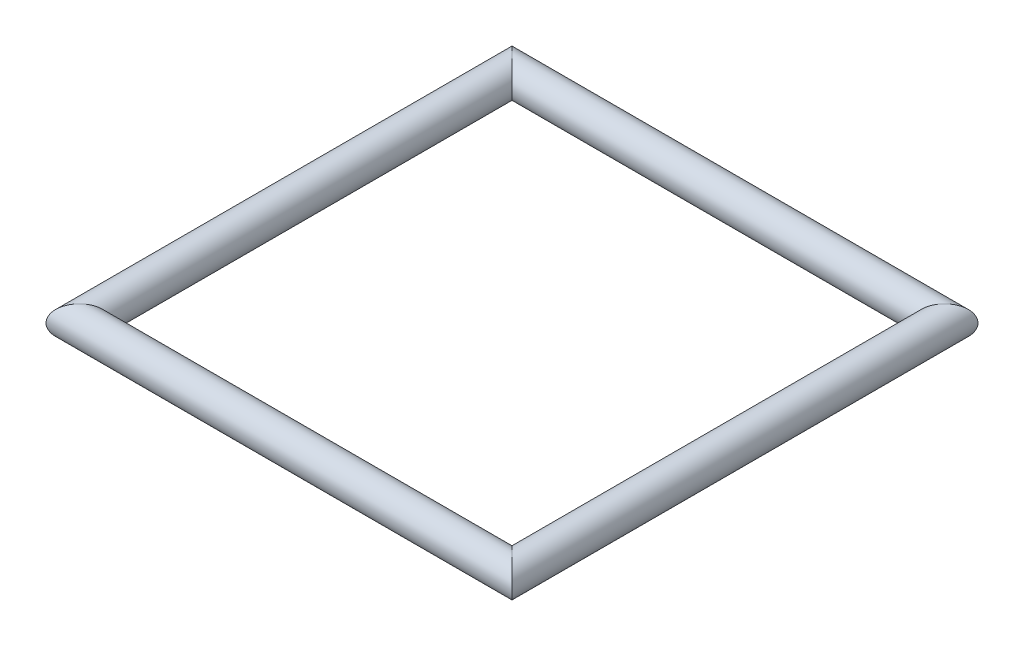
SolidWorks part; units mm, degrees
ref_plane "Front Plane" through (0, 0, 0) normal (0, 0, 1) x (1, 0, 0)
ref_plane "Top Plane" through (0, 0, 0) normal (0, 1, 0) x (1, 0, 0)
ref_plane "Right Plane" through (0, 0, 0) normal (1, 0, 0) x (0, 0, -1)
sketch "Sketch1" plane through (0, 0, 0) normal (0, 1, 0) x (1, 0, 0)
  line L1 (-650, 650) -> (650, 650)
  line L2 (-650, 650) -> (-650, -650)
  line L3 (-650, -650) -> (650, -650)
  line L4 (650, 650) -> (650, -650)
  line L5 (-650, 650) -> (650, -650) construction
  line L6 (-650, -650) -> (650, 650) construction
  point P0 (0, 0)
  dimension "D1" = 1300
  dimension "D2" = 1300
sweep "Sweep1" add path "Sketch1" circular profile diameter 100 parameters "D3"=100
sketch3d "URDF Reference"
  line L0 (0, 0, 0) -> (10, 0, 0) construction
  line L1 (0, 0, 0) -> (0, 0, -10) construction
  point P0 (0, 0, 0)
  point P1 (0, 0, 0)
